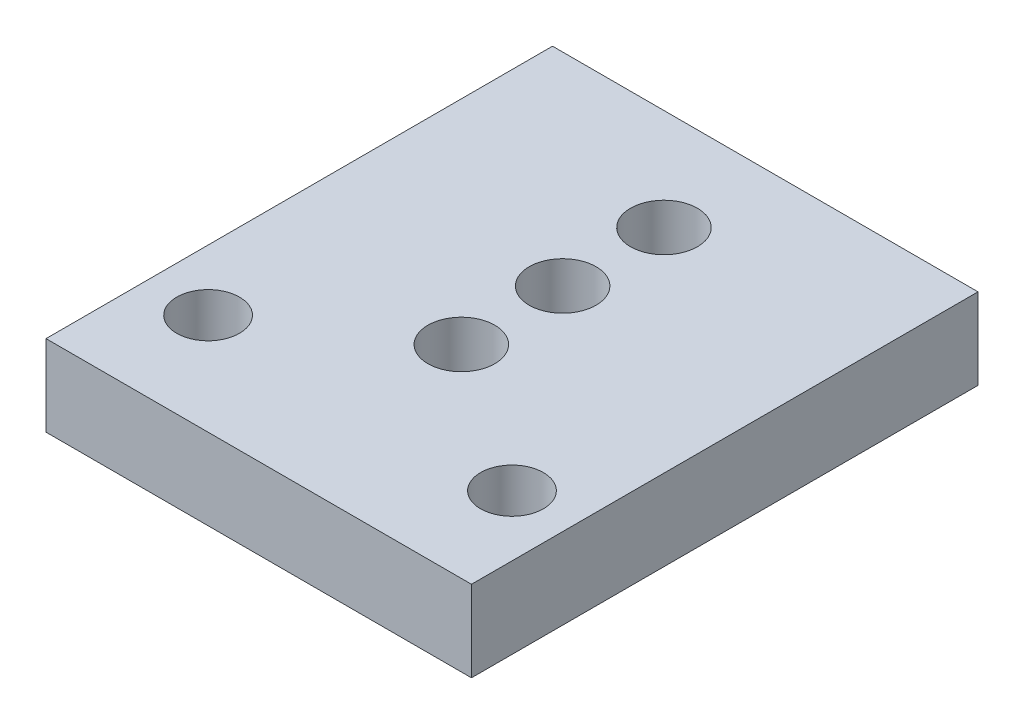
SolidWorks part; units mm, degrees
material "6061-T6 (SS)"
ref_plane "Front Plane" through (0, 0, 0) normal (0, 0, 1) x (1, 0, 0)
ref_plane "Top Plane" through (0, 0, 0) normal (0, 1, 0) x (1, 0, 0)
ref_plane "Right Plane" through (0, 0, 0) normal (1, 0, 0) x (0, 0, -1)
sketch "Sketch1" plane through (0, 0, 0) normal (0, 1, 0) x (1, 0, 0)
  line L1 (0, 0) -> (21, 0)
  line L2 (0, 0) -> (0, 25)
  line L3 (0, 25) -> (21, 25)
  line L4 (21, 0) -> (21, 25)
  dimension "D1" = 25
  dimension "D2" = 21
extrude "Boss-Extrude1" add sketch "Sketch1" along normal blind 4
hole_wizard "Ø3.1 (3.1) Diameter Hole1" positions "Sketch3" profile "Sketch4" hole size "Ø3.1" standard "ANSI Metric"
sketch "Sketch3" plane through (0, 4, 0) normal (0, 1, 0) x (1, 0, 0)
  line L0 (0, 0) -> (21, 0) construction
  line L2 (0, 25) -> (0, 0) construction
  point P2 (3, 5)
  point P16 (18, 5)
  dimension "D1" = 15
  dimension "D4" = 5
  dimension "D5" = 3
sketch "Sketch4" plane through (3, 4, -5) normal (1, 0, 0) x (0, 0, 1)
  line L0 (0, 0) -> (0, 10.9313)
  line L1 (0, 10.9313) -> (1.55, 10)
  line L2 (1.55, 10) -> (1.55, 0)
  line L5 (1.55, 0) -> (0, 0)
  line L10 (0, 10.9313) -> (-1.55, 10) construction
  line L11 (0, -6.35) -> (0, 107.95) construction
  dimension "Hole Dia." = 3.1
  dimension "Hole Depth" = 10
  dimension "Drill Angle" = 118
hole_wizard "M4x0.7 Tapped Hole1" positions "Sketch13" profile "Sketch14" tap size "M4x0.7" standard "ANSI Metric" end condition through all
sketch "Sketch13" plane through (0, 4, 0) normal (0, 1, 0) x (1, 0, 0)
  line L0 (10.5, 25) -> (10.5, 0) construction
  line L1 (21, 25) -> (0, 25) construction
  line L2 (0, 0) -> (21, 0) construction
  point P9 (10.5, 20)
  point P11 (10.5, 15)
  point P13 (10.5, 10)
  dimension "D1" = 10
  dimension "D2" = 5
  dimension "D3" = 5
sketch "Sketch14" plane through (10.5, 4, -10) normal (1, 0, 0) x (0, 0, 1)
  line L0 (0, 0) -> (0, 4)
  line L1 (0, 4) -> (1.65, 4)
  line L2 (1.65, 4) -> (1.65, 0)
  line L5 (1.65, 0) -> (0, 0)
  line L11 (0, -6.35) -> (0, 107.95) construction
  dimension "Thru Tap Drill Dia." = 3.3
  dimension "Thru Tap Drill Depth" = 4
cosmetic thread "Hole Thread4"
cosmetic thread "Hole Thread5"
cosmetic thread "Hole Thread6"
